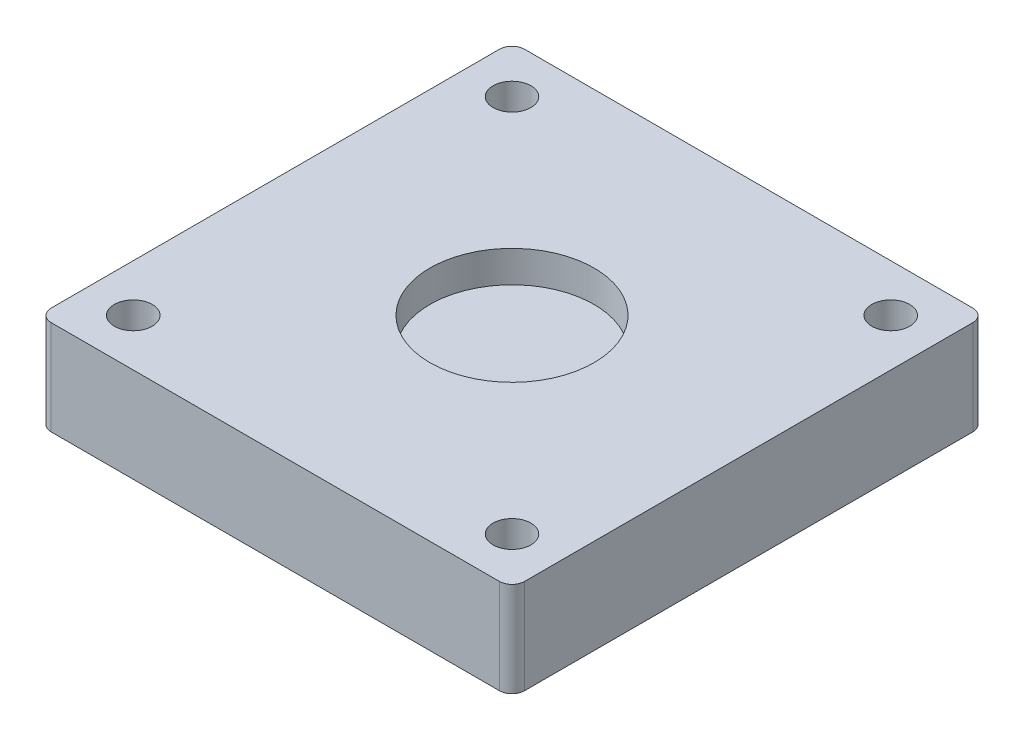
SolidWorks part; units mm, degrees
ref_plane "Front Plane" through (0, 0, 0) normal (0, 0, 1) x (1, 0, 0)
ref_plane "Top Plane" through (0, 0, 0) normal (0, 1, 0) x (1, 0, 0)
ref_plane "Right Plane" through (0, 0, 0) normal (1, 0, 0) x (0, 0, -1)
sketch "Sketch1" plane through (0, 0, 0) normal (0, 0, 1) x (1, 0, 0)
  line L1 (-37.5, 7.5) -> (37.5, 7.5)
  line L2 (-37.5, 7.5) -> (-37.5, -7.5)
  line L3 (-37.5, -7.5) -> (37.5, -7.5)
  line L4 (37.5, 7.5) -> (37.5, -7.5)
  line L5 (-37.5, 7.5) -> (37.5, -7.5) construction
  line L6 (-37.5, -7.5) -> (37.5, 7.5) construction
  point P0 (0, 0)
  dimension "D1" = 75
  dimension "D2" = 15
extrude "Boss-Extrude1" add sketch "Sketch1" along normal mid plane 75
sketch "Sketch2" plane through (0, 7.5, 0) normal (0, 1, 0) x (1, 0, 0)
  line L0 (0, 0) -> (0, -50000) construction
  line L1 (0, 0) -> (50000, 0) construction
  circle A0 centre (0, 0) radius 13
  circle A1 centre (-30, 30) radius 3
  circle A2 centre (-30, -30) radius 3
  circle A3 centre (30, -30) radius 3
  circle A4 centre (30, 30) radius 3
  dimension "D1" = 26
  dimension "D2" = 6
  dimension "D3" = 30
  dimension "D4" = 30
extrude "Cut-Extrude1" cut sketch "Sketch2" against normal blind 5
sketch "Sketch3" plane through (0, 2.5, 0) normal (0, 1, 0) x (1, 0, 0)
  circle A0 centre (-30, 30) radius 2
  circle A1 centre (30, 30) radius 2
  circle A2 centre (30, -30) radius 2
  circle A3 centre (-30, -30) radius 2
  dimension "D1" = 4
  dimension "D2" = 4
extrude "Cut-Extrude2" cut sketch "Sketch3" against normal through all
fillet "Fillet1" radius 2 4 edges at (37.5, 0, 37.5) (37.5, 0, -37.5) (-37.5, 0, -37.5) (-37.5, 0, 37.5)
